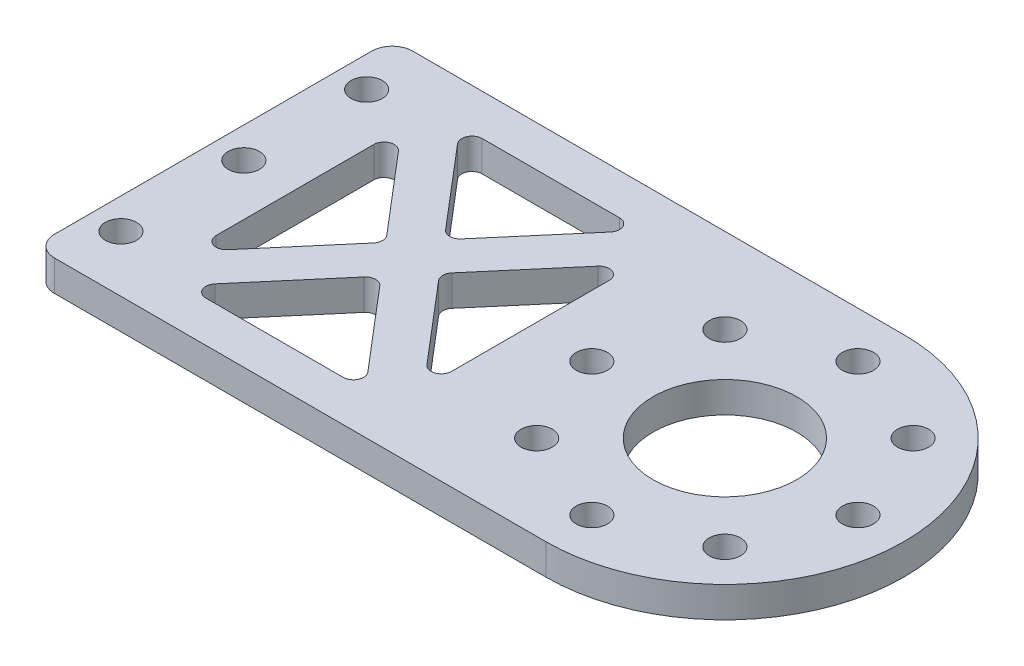
SolidWorks part; units mm, degrees
material "Thornel Mat VMA"
ref_plane "前视基准面" through (0, 0, 0) normal (0, 0, 1) x (1, 0, 0)
ref_plane "上视基准面" through (0, 0, 0) normal (0, 1, 0) x (1, 0, 0)
ref_plane "右视基准面" through (0, 0, 0) normal (1, 0, 0) x (0, 0, -1)
other "Configuration Table"
sketch "草图1" plane through (0, 0, 0) normal (0, 1, 0) x (1, 0, 0)
  line L1 (-25, -17.5) -> (25, -17.5)
  line L2 (-25, -17.5) -> (-25, 17.5)
  line L3 (-25, 17.5) -> (25, 17.5)
  line L4 (25, -17.5) -> (25, 17.5)
  line L5 (-25, -17.5) -> (25, 17.5) construction
  line L6 (-25, 17.5) -> (25, -17.5) construction
  circle A1 centre (25, 0) radius 17.5
  point P0 (0, 0)
  dimension "D1" = 35
  dimension "D2" = 35
  dimension "D3" = 50
extrude "凸台-拉伸1" add sketch "草图1" along normal blind 3 contours A1 L3 L2 L1 | L3 A1 L1 L4 | L1 A1 L3 L4
sketch "草图2" plane through (0, 3, 0) normal (0, 1, 0) x (1, 0, 0)
  circle A0 centre (25, 0) radius 7.025
  dimension "D1" = 14.05
extrude "切除-拉伸1" cut sketch "草图2" against normal through all
sketch "草图4" plane through (0, 3, 0) normal (0, 1, 0) x (1, 0, 0)
  circle A0 centre (25, 0) radius 13 construction
  circle A1 centre (25, 13) radius 1.525
  circle A2 centre (34.1924, 9.1924) radius 1.525
  circle A3 centre (38, 0) radius 1.525
  circle A4 centre (34.1924, -9.1924) radius 1.525
  circle A5 centre (25, -13) radius 1.525
  circle A6 centre (15.8076, -9.1924) radius 1.525
  circle A7 centre (12, 0) radius 1.525
  circle A8 centre (15.8076, 9.1924) radius 1.525
  point P21 (25, 0)
  dimension "D1" = 26
  dimension "D2" = 3.05
  dimension "D3" = 8
extrude "切除-拉伸3" cut sketch "草图4" against normal through all
sketch "草图5" plane through (0, 3, 0) normal (0, 1, 0) x (1, 0, 0)
  line L0 (-25, -17.5) -> (-25, 17.5) construction
  line L1 (-15, -12.5) -> (5, -12.5)
  line L2 (-15, -12.5) -> (-15, 12.5)
  line L3 (-15, 12.5) -> (5, 12.5)
  line L4 (5, -12.5) -> (5, 12.5)
  line L5 (-15, -12.5) -> (5, 12.5) construction
  line L6 (-15, 12.5) -> (5, -12.5) construction
  line L7 (-25, 17.5) -> (25, 17.5) construction
  line L8 (-16.3275, 11.438) -> (3.6725, -13.562)
  line L9 (-13.6725, -13.562) -> (6.3275, 11.438)
  line L10 (-13.6725, 13.562) -> (6.3275, -11.438)
  line L11 (-16.3275, -11.438) -> (3.6725, 13.562)
  point P0 (-5, 0)
  dimension "D1" = 10
  dimension "D2" = 20
  dimension "D3" = 5
  dimension "D4" = 1.7
  dimension "D5" = 1.7
fillet "圆角2" radius 2 2 edges at (-25, 1.5, -17.5) (-25, 1.5, 17.5)
sketch "草图7" plane through (0, 3, 0) normal (0, 1, 0) x (1, 0, 0)
  line L0 (-25, -15.5) -> (-25, 15.5) construction
  line L1 (-17, -13.5) -> (6, -13.5)
  line L2 (-17, -13.5) -> (-17, 13.5)
  line L3 (-17, 13.5) -> (6, 13.5)
  line L4 (6, -13.5) -> (6, 13.5)
  line L5 (-17, -13.5) -> (6, 13.5) construction
  line L6 (-17, 13.5) -> (6, -13.5) construction
  line L7 (-23, 17.5) -> (25, 17.5) construction
  line L8 (-18.5225, 12.2031) -> (4.4775, -14.7969)
  line L9 (-15.4775, -14.7969) -> (7.5225, 12.2031)
  line L10 (-15.4775, 14.7969) -> (7.5225, -12.2031)
  line L11 (-18.5225, -12.2031) -> (4.4775, 14.7969)
  circle A0 centre (-5.5, 0) radius 2.5
  point P0 (-5.5, 0)
  dimension "D4" = 5
  dimension "D1" = 8
  dimension "D2" = 4
  dimension "D3" = 23
  dimension "D5" = 2
  dimension "D6" = 2
extrude "切除-拉伸6" cut sketch "草图7" against normal through all contours L10 L11 L3 | L9 L10 L4 | L9 L1 L8 | L2 L11 L8
sketch "草图10" plane through (0, 3, 0) normal (0, 1, 0) x (1, 0, 0)
  line L0 (-22, 8.7452) -> (-22, 50008.7452) construction
  line L1 (-25, -15.5) -> (-25, 15.5) construction
  line L2 (-22, 0) -> (49978, 0) construction
  circle A0 centre (-22, 0) radius 1.525
  circle A1 centre (-22, 12) radius 1.525
  circle A2 centre (-22, -12) radius 1.525
  dimension "D2" = 3.05
  dimension "D1" = 3
  dimension "D3" = 12
extrude "切除-拉伸8" cut sketch "草图10" against normal through all
fillet "圆角7" radius 1 12 edges at (-5.5, 1.5, 3.0842) (3.3727, 1.5, 13.5) (-14.3727, 1.5, 13.5) (-8.1273, 1.5, 0) (-17, 1.5, 10.4158) (3.3727, 1.5, -13.5) (-5.5, 1.5, -3.0842) (-14.3727, 1.5, -13.5) (6, 1.5, -10.4158) (6, 1.5, 10.4158) (-2.8727, 1.5, 0) (-17, 1.5, -10.4158)
